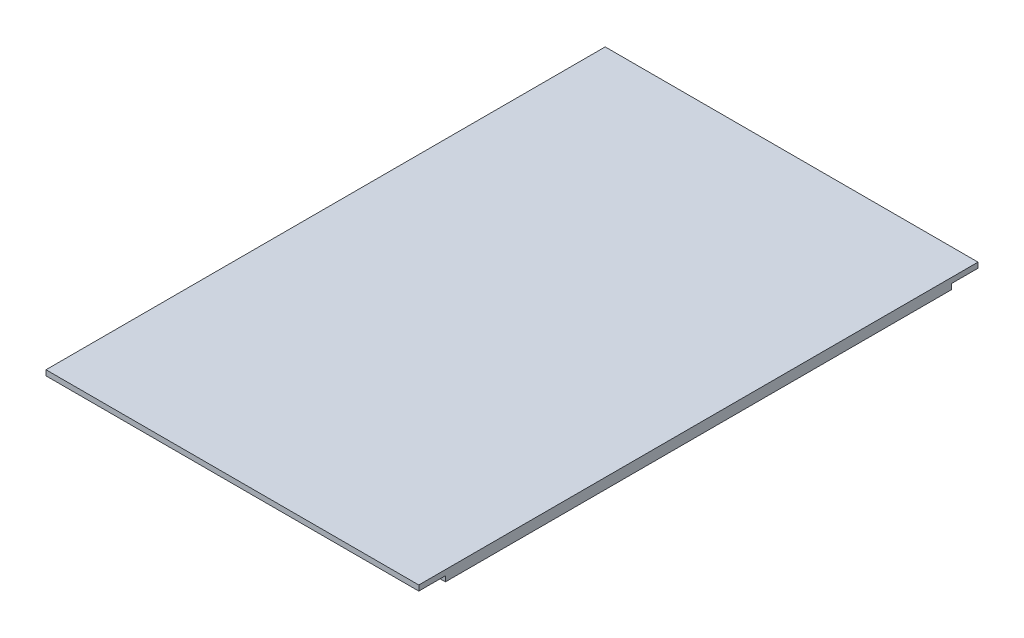
SolidWorks part; units mm, degrees
ref_plane "Front Plane" through (0, 0, 0) normal (0, 0, 1) x (1, 0, 0)
ref_plane "Top Plane" through (0, 0, 0) normal (0, 1, 0) x (1, 0, 0)
ref_plane "Right Plane" through (0, 0, 0) normal (1, 0, 0) x (0, 0, -1)
sketch "Sketch2" plane through (0, 0, 0) normal (0, 1, 0) x (1, 0, 0)
  line L0 (-70, 70) -> (70, 70) construction
  line L1 (-70, 210) -> (70, 210)
  line L2 (-70, 210) -> (-70, -210)
  line L3 (-70, -210) -> (70, -210)
  line L4 (70, 210) -> (70, -210)
  line L5 (-70, 210) -> (70, -210) construction
  line L6 (-70, -210) -> (70, 210) construction
  point P0 (0, 0)
  dimension "D1" = 420
  dimension "D2" = 140
  dimension "D3" = 280
extrude "Boss-Extrude1" add sketch "Sketch2" along normal blind 4
sketch "Sketch3" plane through (0, 4, 0) normal (0, 1, 0) x (1, 0, 0)
  line L0 (0, 0) -> (0, -210) construction
  line L1 (-37.5, -165) -> (-37.5, -145)
  line L2 (-37.5, -145) -> (-43.5, -145)
  line L3 (-43.5, -145) -> (-43.5, -165)
  line L4 (70, -210) -> (70, 210)
  line L5 (70, 210) -> (-70, 210)
  line L6 (-70, 210) -> (-70, -210)
  line L7 (-70, -210) -> (70, -210)
  line L8 (70, -210) -> (70, 210)
  line L9 (70, 210) -> (-70, 210)
  line L10 (-70, 210) -> (-70, -210)
  line L11 (-70, -210) -> (70, -210)
  line L12 (37.5, -165) -> (37.5, -145)
  line L13 (37.5, -145) -> (43.5, -145)
  line L14 (43.5, -145) -> (43.5, -165)
  line L15 (-37.5, -165) -> (37.5, -165) construction
  arc A0 (-37.5, -165) -> (37.5, -165) centre (0, -165) ccw
  arc A1 (-43.5, -165) -> (43.5, -165) centre (0, -165) ccw
  dimension "D2" = 37.5
  dimension "D3" = 6
  dimension "D4" = 6
  dimension "D5" = 45
  dimension "D6" = 6
  dimension "D7" = 20
  dimension "D8" = 20
  dimension "D1" = 0
extrude "Boss-Extrude2" add sketch "Sketch3" along normal blind 25 contours L3 A1 L14 L13 L12 A0 L1 L2
sketch "Sketch4" plane through (0, 4, 0) normal (0, 1, 0) x (1, 0, 0)
  line L1 (-65, 180) -> (-54.75, 180)
  line L2 (-65, 180) -> (-65, 99.75)
  line L3 (-65, 99.75) -> (-54.75, 99.75)
  line L4 (-54.75, 180) -> (-54.75, 99.75)
  line L5 (-65, 180) -> (-54.75, 99.75) construction
  line L6 (-65, 99.75) -> (-54.75, 180) construction
  line L7 (54.75, 180) -> (65, 180)
  line L8 (54.75, 180) -> (54.75, 99.75)
  line L9 (54.75, 99.75) -> (65, 99.75)
  line L10 (65, 180) -> (65, 99.75)
  line L11 (54.75, 180) -> (65, 99.75) construction
  line L12 (54.75, 99.75) -> (65, 180) construction
  line L13 (-70, 210) -> (70, 210) construction
  line L14 (-70, 210) -> (-70, -210) construction
  line L15 (70, 210) -> (70, -210) construction
  point P4 (-59.875, 139.875)
  point P9 (59.875, 139.875)
  dimension "D1" = 10.25
  dimension "D2" = 10.25
  dimension "D3" = 80.25
  dimension "D4" = 80.25
  dimension "D5" = 30
  dimension "D6" = 30
  dimension "D7" = 5
  dimension "D8" = 5
extrude "Cut-Extrude1" cut sketch "Sketch4" against normal blind 25.4
sketch "Sketch6" plane through (0, 4, 0) normal (0, 1, 0) x (1, 0, 0)
  line L0 (-65, 99.75) -> (-54.75, 99.75) construction
  line L1 (-65, 99.75) -> (-54.75, 99.75)
  line L2 (0, -202.5) -> (0, 99.75) construction
  line L3 (0, 99.75) -> (-54.75, 99.75) construction
  arc A0 (-37.5, -165) -> (37.5, -165) centre (0, -165) ccw construction
  arc A1 (-37.5, -165) -> (37.5, -165) centre (0, -165) ccw
  point P5 (0, -202.5)
  dimension "D1" = 302.25
sketch "Sketch7" plane through (0, 4, 0) normal (0, 1, 0) x (1, 0, 0)
  line L0 (70, 210) -> (-70, 210) construction
  line L1 (-65, 205) -> (65, 205)
  line L2 (-65, 205) -> (-65, 195)
  line L3 (-65, 195) -> (65, 195)
  line L4 (65, 205) -> (65, 195)
  line L5 (-65, 205) -> (65, 195) construction
  line L6 (-65, 195) -> (65, 205) construction
  line L7 (-70, 210) -> (-70, -210) construction
  line L8 (70, -210) -> (70, 210) construction
  point P4 (0, 200)
  dimension "D1" = 5
  dimension "D2" = 5
  dimension "D3" = 5
  dimension "D4" = 10
extrude "Cut-Extrude2" cut sketch "Sketch7" against normal blind 2.45 contours L3 L4 L1 L2
sketch "Sketch9" plane through (0, 0, 0) normal (0, -1, 0) x (1, 0, 0)
  line L0 (-70, 95) -> (70, 95)
  line L1 (-70, -95) -> (70, -95)
  line L4 (70, -210) -> (70, 210)
  line L5 (70, 210) -> (-70, 210)
  line L6 (-70, 210) -> (-70, -210)
  line L7 (-70, -210) -> (70, -210)
  line L8 (70, -210) -> (70, 210)
  line L9 (70, 210) -> (-70, 210)
  line L10 (-70, 210) -> (-70, -210)
  line L11 (-70, -210) -> (70, -210)
  line M7 (-54.75, -180) -> (-65, -180)
  line M8 (-65, -180) -> (-65, -99.75)
  line M9 (-65, -99.75) -> (-54.75, -99.75)
  line M10 (-54.75, -99.75) -> (-54.75, -180)
  line M11 (65, -180) -> (54.75, -180)
  line M12 (54.75, -180) -> (54.75, -99.75)
  line M13 (54.75, -99.75) -> (65, -99.75)
  line M14 (65, -99.75) -> (65, -180)
  line M15 (70, -210) -> (70, 210)
  line M16 (70, 210) -> (-70, 210)
  line M17 (-70, 210) -> (-70, -210)
  line M18 (-70, -210) -> (70, -210)
  dimension "D2" = 115
  dimension "D3" = 115
  dimension "D1" = 0
extrude "Cut-Extrude3" cut sketch "Sketch9" against normal through all and the other way through all contours L0 M17 M15 M16 | L1 M17 M18 M15 M14 M11 M12 M13 M10 M7 M8 M9
sketch "Sketch10" plane through (0, 4, 0) normal (0, 1, 0) x (1, 0, 0)
  line L0 (70, -95) -> (70, 95) construction
  line L1 (-70, 95) -> (70, 95)
  line L2 (-70, 95) -> (-70, 105)
  line L3 (-70, 105) -> (70, 105)
  line L4 (70, 95) -> (70, 105)
  line L5 (-70, 95) -> (70, 105) construction
  line L6 (-70, 105) -> (70, 95) construction
  line L7 (-70, -95) -> (70, -95)
  line L8 (-70, -95) -> (-70, -105)
  line L9 (-70, -105) -> (70, -105)
  line L10 (70, -95) -> (70, -105)
  line L11 (-70, -95) -> (70, -105) construction
  line L12 (-70, -105) -> (70, -95) construction
  point P4 (0, 100)
  point P10 (0, -100)
  dimension "D1" = 10
  dimension "D2" = 10
extrude "Boss-Extrude3" add sketch "Sketch10" against normal blind 2
